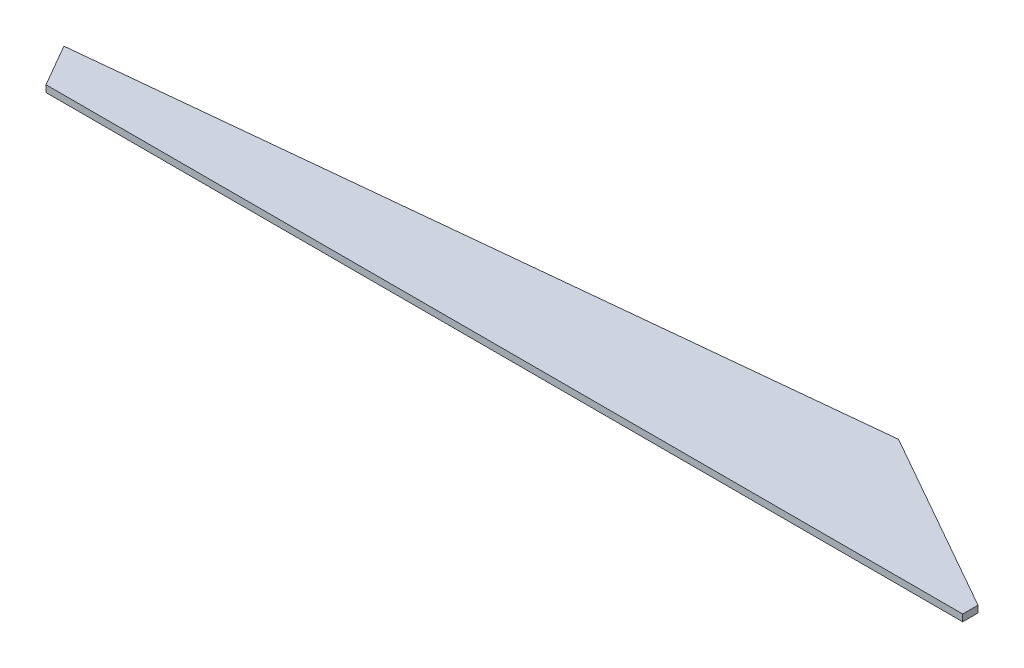
SolidWorks part; units mm, degrees
ref_plane "Front Plane" through (0, 0, 0) normal (0, 0, 1) x (1, 0, 0)
ref_plane "Top Plane" through (0, 0, 0) normal (0, 1, 0) x (1, 0, 0)
ref_plane "Right Plane" through (0, 0, 0) normal (1, 0, 0) x (0, 0, -1)
sketch "Sketch1" plane through (0, 0, 0) normal (0, 1, 0) x (1, 0, 0)
  line L0 (0, 0) -> (-6750, 0)
  line L1 (0, 0) -> (-1350, 0)
  line L2 (-1350, 0) -> (-1350, 877.5)
  line L3 (0, 0) -> (0, 112.5)
  line L4 (-1350, 877.5) -> (0, 112.5)
  line L5 (-6750, 0) -> (-6930, 311.7691)
  line L6 (-6930, 311.7691) -> (-1350, 877.5)
  line L7 (-2272.9163, -333.2324) -> (-2572.5172, 449.2127) construction
  line L8 (9284.6178, 3455.3596) -> (9947.2845, 3455.3596) construction
extrude "Boss-Extrude1" add sketch "Sketch1" along normal blind 50 contours L4 L2 L0 L3 | L6 L5 L0 L2
